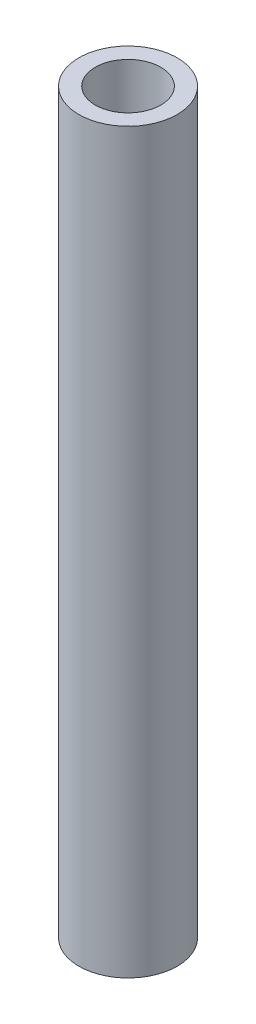
SolidWorks part; units mm, degrees
material "acero"
ref_plane "Alzado" through (0, 0, 0) normal (0, 0, 1) x (1, 0, 0)
ref_plane "Planta" through (0, 0, 0) normal (0, 1, 0) x (1, 0, 0)
ref_plane "Vista lateral" through (0, 0, 0) normal (1, 0, 0) x (0, 0, -1)
sketch "Croquis1" plane through (0, 0, 0) normal (0, 0, 1) x (1, 0, 0)
  line L0 (0, -0.7202) -> (0, 0.7202)
  line L2 (3, -22.5) -> (-3, -22.5)
  line L3 (3, -22.5) -> (3, 22.5)
  line L4 (3, 22.5) -> (-3, 22.5)
  line L5 (-3, -22.5) -> (-3, 22.5)
  line L6 (3, -22.5) -> (-3, 22.5) construction
  line L7 (3, 22.5) -> (-3, -22.5) construction
  line L8 (2, -22.5) -> (-2, -22.5)
  line L9 (2, -22.5) -> (2, 22.5)
  line L10 (2, 22.5) -> (-2, 22.5)
  line L11 (-2, -22.5) -> (-2, 22.5)
  line L12 (2, -22.5) -> (-2, 22.5) construction
  line L13 (2, 22.5) -> (-2, -22.5) construction
  point P1 (0, 0)
  point P3 (0, 0)
  dimension "D1" = 6
  dimension "D2" = 4
  dimension "D3" = 45
revolve "Revolución1" add sketch "Croquis1" angle 360 about L0
